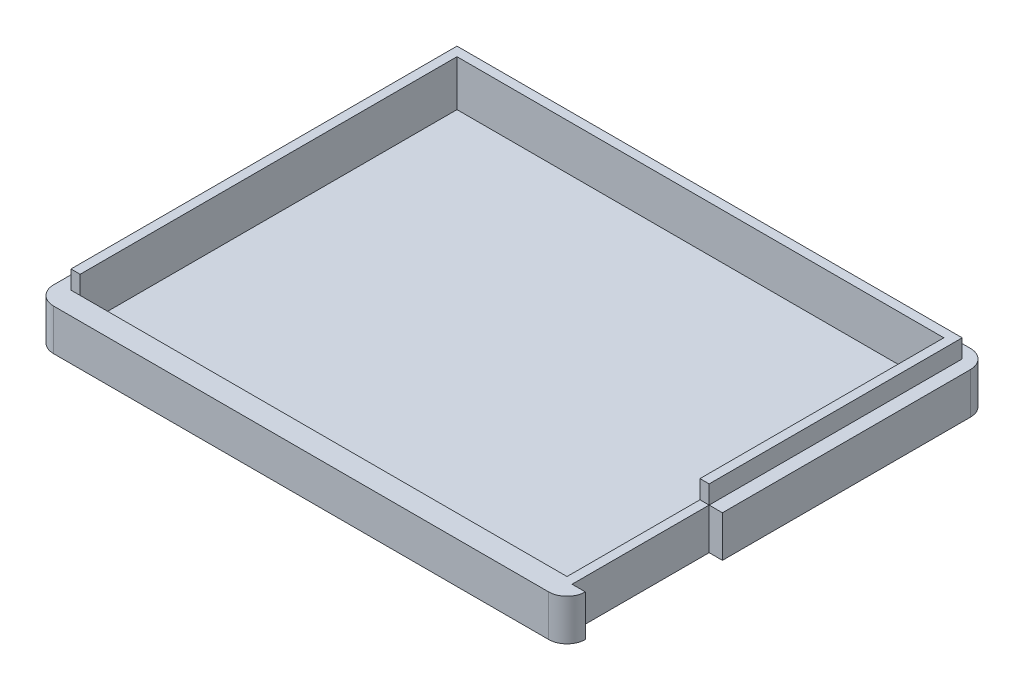
SolidWorks part; units mm, degrees
ref_plane "Front Plane" through (0, 0, 0) normal (0, 0, 1) x (1, 0, 0)
ref_plane "Top Plane" through (0, 0, 0) normal (0, 1, 0) x (1, 0, 0)
ref_plane "Right Plane" through (0, 0, 0) normal (1, 0, 0) x (0, 0, -1)
sketch "Sketch1" plane through (0, 0, 0) normal (0, 1, 0) x (1, 0, 0)
  line L1 (-26.0701, -28.5402) -> (31.9299, -28.5402)
  line L2 (-26.0701, -28.5402) -> (-26.0701, 17.4598)
  line L3 (-26.0701, 17.4598) -> (31.9299, 17.4598)
  line L4 (31.9299, -28.5402) -> (31.9299, 17.4598)
  dimension "D1" = 58
  dimension "D2" = 46
extrude "Boss-Extrude1" add sketch "Sketch1" along normal blind 4.5
sketch "Sketch2" plane through (0, 4.5, 0) normal (0, 1, 0) x (1, 0, 0)
  line L0 (31.9299, 17.4598) -> (-26.0701, 17.4598) construction
  line L1 (-24.6201, 16.0098) -> (30.4799, 16.0098)
  line L2 (-24.6201, 16.0098) -> (-24.6201, -27.0902)
  line L3 (-24.6201, -27.0902) -> (30.4799, -27.0902)
  line L4 (30.4799, 16.0098) -> (30.4799, -27.0902)
  line L5 (-23.6201, 15.0098) -> (29.4799, 15.0098)
  line L6 (-23.6201, 15.0098) -> (-23.6201, -26.0902)
  line L7 (-23.6201, -26.0902) -> (29.4799, -26.0902)
  line L8 (29.4799, 15.0098) -> (29.4799, -26.0902)
  line L9 (-26.0701, 17.4598) -> (-26.0701, -28.5402) construction
  line L10 (31.9299, -28.5402) -> (31.9299, 17.4598) construction
  line L11 (-26.0701, -28.5402) -> (31.9299, -28.5402) construction
  dimension "D1" = 1
  dimension "D2" = 1
  dimension "D3" = 1
  dimension "D4" = 1
  dimension "D5" = 1.45
  dimension "D6" = 1.45
  dimension "D7" = 1.45
  dimension "D8" = 1.45
extrude "Boss-Extrude2" add sketch "Sketch2" along normal blind 2
sketch "Sketch3" plane through (0, 4.5, 0) normal (0, 1, 0) x (1, 0, 0)
  line L1 (-23.6201, -26.0902) -> (29.4799, -26.0902)
  line L2 (-23.6201, -26.0902) -> (-23.6201, 15.0098)
  line L3 (-23.6201, 15.0098) -> (29.4799, 15.0098)
  line L4 (29.4799, -26.0902) -> (29.4799, 15.0098)
extrude "Cut-Extrude1" cut sketch "Sketch3" against normal blind 3
sketch "Sketch4" plane through (0, 6.5, 0) normal (0, 1, 0) x (1, 0, 0)
  line L0 (29.4799, -26.0902) -> (29.4799, 15.0098) construction
  line L1 (30.4799, -27.0902) -> (29.4799, -27.0902)
  line L2 (30.4799, -27.0902) -> (30.4799, -11.5902)
  line L3 (30.4799, -11.5902) -> (29.4799, -11.5902)
  line L4 (29.4799, -27.0902) -> (29.4799, -11.5902)
  dimension "D1" = 15.5
extrude "Cut-Extrude2" cut sketch "Sketch4" against normal blind 2
sketch "Sketch5" plane through (0, 1.5, 0) normal (0, 1, 0) x (1, 0, 0)
  line L1 (-24.6201, -27.0902) -> (29.4799, -27.0902)
  line L2 (-24.6201, -27.0902) -> (-24.6201, -26.0902)
  line L3 (-24.6201, -26.0902) -> (29.4799, -26.0902)
  line L4 (29.4799, -27.0902) -> (29.4799, -26.0902)
extrude "Cut-Extrude4" cut sketch "Sketch5" against normal blind 2 from surface at 5 starting at face at (8.2399, 6.5, 6.7502)
fillet "Fillet1" radius 2 4 edges at (-26.0701, 2.25, 28.5402) (31.9299, 2.25, 28.5402) (31.9299, 2.25, -17.4598) (-26.0701, 2.25, -17.4598)
sketch "Sketch6" plane through (0, 4.5, 0) normal (0, 1, 0) x (1, 0, 0)
  line L1 (30.4799, -11.5902) -> (31.9299, -11.5902)
  line L2 (30.4799, -11.5902) -> (30.4799, -26.5402)
  line L3 (30.4799, -26.5402) -> (31.9299, -26.5402)
  line L4 (31.9299, -11.5902) -> (31.9299, -26.5402)
extrude "Cut-Extrude5" cut sketch "Sketch6" against normal through all
